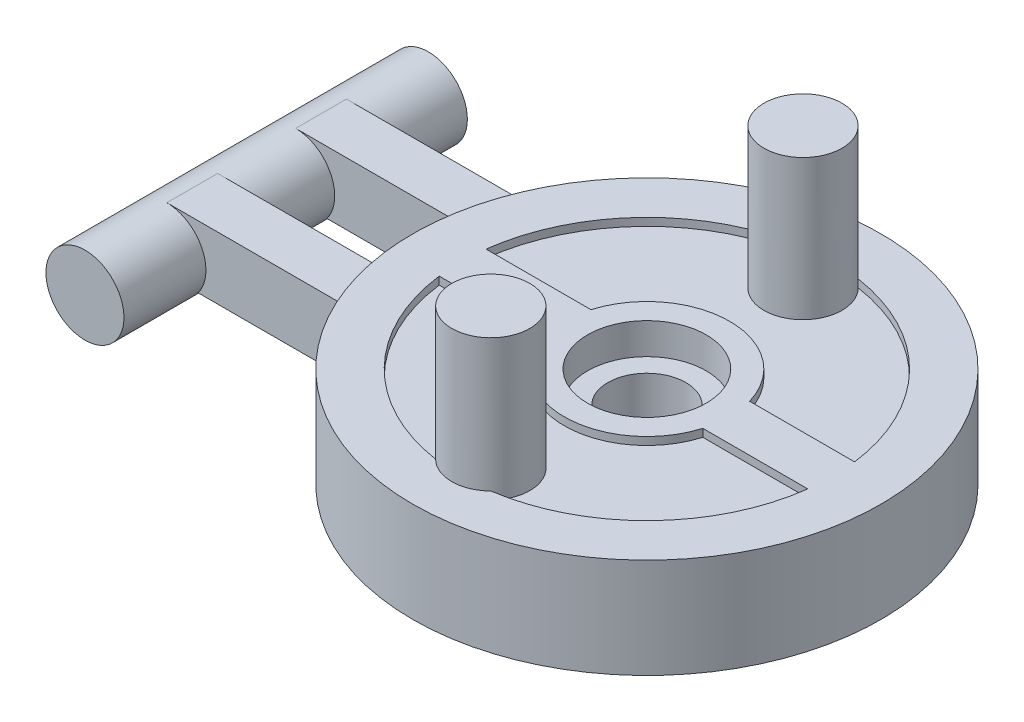
SolidWorks part; units mm, degrees
material "ABS"
ref_plane "Front Plane" through (0, 0, 0) normal (0, 0, 1) x (1, 0, 0)
ref_plane "Top Plane" through (0, 0, 0) normal (0, 1, 0) x (1, 0, 0)
ref_plane "Right Plane" through (0, 0, 0) normal (1, 0, 0) x (0, 0, -1)
sketch "Sketch1" plane through (0, 0, 0) normal (0, 1, 0) x (1, 0, 0)
  circle A0 centre (0, 0) radius 15
  dimension "D1" = 30
extrude "Boss-Extrude1" add sketch "Sketch1" along normal blind 6.4 contours A0
sketch "Sketch2" plane through (0, 6.4, 0) normal (0, 1, 0) x (1, 0, 0)
  line L0 (5.0833, -1.5) -> (11.8051, -1.5)
  line L1 (-3.52, 0) -> (3.52, 0) construction
  line L4 (-11.8051, -1.5) -> (-5.0833, -1.5)
  line L5 (5.0833, 1.5) -> (11.8051, 1.5)
  line L6 (-11.8051, 1.5) -> (-5.0833, 1.5)
  arc A0 (-11.8051, -1.5) -> (11.8051, -1.5) centre (0, 0) ccw
  arc A1 (-5.0833, -1.5) -> (5.0833, -1.5) centre (0, 0) ccw
  arc A2 (-11.8051, 1.5) -> (-11.8066, 1.4882) centre (0, 0) ccw
  arc A3 (11.8066, 1.4882) -> (11.8051, 1.5) centre (0, 0) ccw
  arc A4 (-11.8051, 1.5) -> (11.8051, 1.5) centre (0, 0) cw
  arc A5 (-5.0833, 1.5) -> (5.0833, 1.5) centre (0, 0) cw
  dimension "D1" = 23.8
  dimension "D2" = 10.6
  dimension "D3" = 1.5
extrude "Cut-Extrude1" cut sketch "Sketch2" against normal blind 0.5 contours A1 L4 A0 L0 | L6 A5 L5 A4
sketch "Sketch3" plane through (0, 5.9, 0) normal (0, 1, 0) x (1, 0, 0)
  line L0 (0, -3.52) -> (0, 3.52) construction
  line L1 (-3.52, 0) -> (3.52, 0) construction
  circle A0 centre (0, -10) radius 2.5
  circle A1 centre (0, 10) radius 2.5
  dimension "D1" = 5
  dimension "D2" = 10
extrude "Boss-Extrude2" add sketch "Sketch3" along normal blind 9
sketch "Sketch4" plane through (0, 6.4, 0) normal (0, 1, 0) x (1, 0, 0)
  circle A0 centre (0, 0) radius 3.8
  dimension "D1" = 7.6
extrude "Cut-Extrude2" cut sketch "Sketch4" against normal blind 2 contours A0
sketch "Sketch5" plane through (0, 4.4, 0) normal (0, 1, 0) x (1, 0, 0)
  circle A0 centre (0, 0) radius 2.5
  dimension "D1" = 5
sketch "Sketch6" plane through (0, 0, 0) normal (0, -1, 0) x (1, 0, 0)
  circle A0 centre (0, 0) radius 4
  dimension "D1" = 8
extrude "Boss-Extrude3" add sketch "Sketch6" along normal blind 1
extrude "Cut-Extrude3" cut sketch "Sketch5" against normal through all
ref_plane "Plane1" through (0, 2, 0) normal (0, 1, 0) x (1, 0, 0)
sketch "Sketch8" plane through (0, 2, 0) normal (0, 1, 0) x (1, 0, 0)
  line L5 (-8.745, 0) -> (8.745, 0) construction
  line L6 (-13, 5.75) -> (-25, 5.75)
  line L8 (-13, 5.75) -> (-13, 2.5)
  line L9 (-13, -5.75) -> (-25, -5.75)
  line L10 (-25, 5.75) -> (-25, 2.5)
  line L11 (-13, 5.75) -> (-16.3913, 2.5) construction
  line L12 (-13, -5.75) -> (-16.3913, -2.5) construction
  line L13 (0, -8.745) -> (0, 8.745) construction
  line L14 (-25, -2.5) -> (-25, -5.75)
  line L15 (-13, -2.5) -> (-25, -2.5)
  line L17 (-13, 2.5) -> (-25, 2.5)
  line L21 (-21.6087, -2.5) -> (-25, -5.75) construction
  line L22 (-21.6087, 2.5) -> (-25, 5.75) construction
  line L23 (-13, -2.5) -> (-13, -5.75)
  point P0 (0, -19)
  point P1 (-19, 0)
  point P10 (-19, 0)
  dimension "D1" = 11.5
  dimension "D2" = 12
  dimension "D3" = 25
  dimension "D4" = 5
extrude "Boss-Extrude4" add sketch "Sketch8" along normal blind 4
sketch "Sketch9" plane through (0, 0, 0) normal (0, 0, 1) x (1, 0, 0)
  line L0 (-13.8542, 6) -> (-25, 6) construction
  line L1 (0, -8.745) -> (0, 8.745) construction
  circle A0 centre (-25, 3.5) radius 2.5
  dimension "D1" = 5
  dimension "D2" = 0
  dimension "D3" = 25
extrude "Boss-Extrude6" add sketch "Sketch9" along normal mid plane 22
